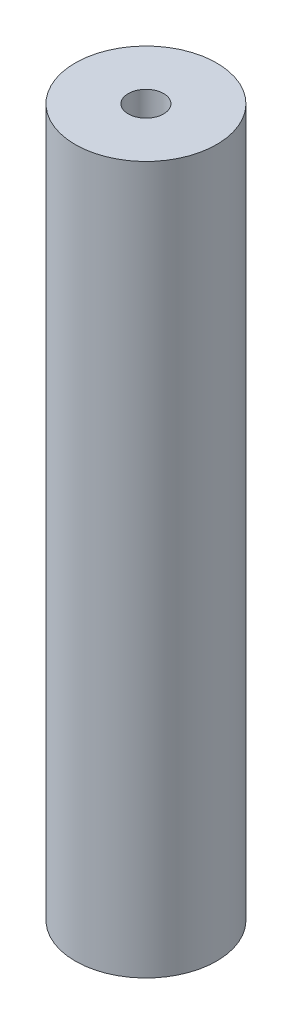
SolidWorks part; units mm, degrees
ref_plane "Front Plane" through (0, 0, 0) normal (0, 0, 1) x (1, 0, 0)
ref_plane "Top Plane" through (0, 0, 0) normal (0, 1, 0) x (1, 0, 0)
ref_plane "Right Plane" through (0, 0, 0) normal (1, 0, 0) x (0, 0, -1)
sketch "Sketch1" plane through (0, 0, 0) normal (0, 1, 0) x (1, 0, 0)
  circle A0 centre (0, 0) radius 100
extrude "Boss-Extrude1" add sketch "Sketch1" along normal blind 1000
sketch "Sketch2" plane through (0, 1000, 0) normal (0, 1, 0) x (1, 0, 0)
  circle A0 centre (0, 0) radius 25
extrude "Cut-Extrude1" cut sketch "Sketch2" against normal blind 50
